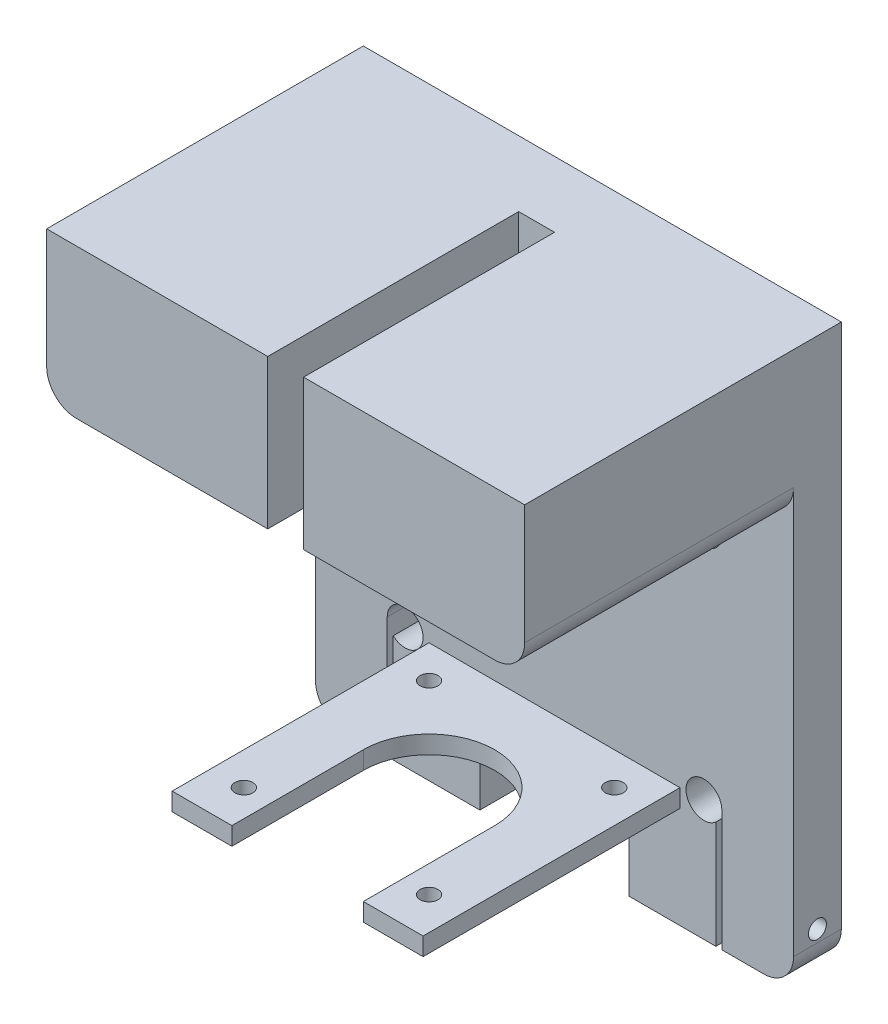
SolidWorks part; units mm, degrees
ref_plane "前视基准面" through (0, 0, 0) normal (0, 0, 1) x (1, 0, 0)
ref_plane "上视基准面" through (0, 0, 0) normal (0, 1, 0) x (1, 0, 0)
ref_plane "右视基准面" through (0, 0, 0) normal (1, 0, 0) x (0, 0, -1)
sketch "草图1" plane through (0, 0, 0) normal (0, 0, 1) x (1, 0, 0)
  line L1 (-40, -42.5) -> (40, -42.5)
  line L2 (-40, -42.5) -> (-40, 42.5)
  line L3 (-40, 42.5) -> (40, 42.5) construction
  line L4 (40, -42.5) -> (40, 42.5)
  line L5 (-40, -42.5) -> (40, 42.5) construction
  line L6 (-40, 42.5) -> (40, -42.5) construction
  line L7 (-40, 42.5) -> (40, 42.5) construction
  line L8 (-40, 42.5) -> (-40, 50.5)
  line L9 (-40, 50.5) -> (40, 50.5)
  line L10 (40, 42.5) -> (40, 50.5)
  point P0 (0, 0)
  dimension "D1" = 80
  dimension "D2" = 85
  dimension "D3" = 8
extrude "凸台-拉伸1" add sketch "草图1" along normal blind 8
sketch "草图3" plane through (0, 0, 8) normal (0, 0, 1) x (1, 0, 0)
  line L0 (0, 43.5088) -> (0, -56.4658) construction
  line L1 (-40, -42.5) -> (40, -42.5) construction
  line L2 (-21, -25.5) -> (21, -25.5)
  line L3 (-21, -25.5) -> (-21, -22.5)
  line L4 (-21, -22.5) -> (21, -22.5)
  line L5 (21, -25.5) -> (21, -22.5)
  line L6 (-21, -25.5) -> (21, -22.5) construction
  line L7 (-21, -22.5) -> (21, -25.5) construction
  point P3 (0, -24)
  dimension "D1" = 17
  dimension "D2" = 3
  dimension "D3" = 42
extrude "凸台-拉伸2" add sketch "草图3" along normal blind 43
sketch "草图4" plane through (0, -25.5, 0) normal (0, -1, 0) x (1, 0, 0)
  line L0 (0, 29) -> (-7.7782, 36.7782) construction
  line L1 (-15.5, 13.5) -> (-14, 13.5) construction
  line L2 (-15.5, 13.5) -> (-15.5, 15) construction
  line L3 (-15.5, 44.5) -> (-14, 44.5) construction
  line L4 (15.5, 13.5) -> (15.5, 15) construction
  line L5 (-15.5, 13.5) -> (-14.4393, 14.5607) construction
  line L6 (-15.5, 44.5) -> (-14.4393, 43.4393) construction
  line L7 (-14, 44.5) -> (14, 44.5) construction
  line L8 (14, 44.5) -> (15.5, 44.5) construction
  line L9 (-7.7782, 36.7782) -> (-14.4393, 43.4393) construction
  line L10 (-14.4393, 43.4393) -> (-15.5, 44.5) construction
  line L11 (-14.4393, 43.4393) -> (-7.7782, 36.7782) construction
  line L12 (0, 29) -> (7.7782, 21.2218) construction
  line L13 (-15.5, 15) -> (-15.5, 43) construction
  line L14 (-15.5, 43) -> (-15.5, 44.5) construction
  line L15 (-14.4393, 14.5607) -> (-7.7782, 21.2218) construction
  line L16 (-7.7782, 21.2218) -> (0, 29) construction
  line L17 (-14, 13.5) -> (14, 13.5) construction
  line L18 (14, 13.5) -> (15.5, 13.5) construction
  line L19 (7.7782, 21.2218) -> (14.4393, 14.5607) construction
  line L20 (14.4393, 14.5607) -> (15.5, 13.5) construction
  line L21 (15.5, 15) -> (15.5, 43) construction
  line L22 (15.5, 43) -> (15.5, 44.5) construction
  line L23 (14.4393, 43.4393) -> (15.5, 44.5) construction
  line L24 (-21, 8) -> (21, 8) construction
  line L26 (-11, 29) -> (-11, 51)
  line L27 (21, 51) -> (21, 8) construction
  line L28 (-21, 51) -> (21, 51) construction
  line L29 (-11, 51) -> (11, 51)
  line L30 (11, 51) -> (11, 29)
  line L31 (-7.7782, 36.7782) -> (0, 29) construction
  line L32 (0, 29) -> (7.7782, 36.7782) construction
  line L33 (7.7782, 36.7782) -> (14.4393, 43.4393) construction
  arc A0 (-11, 29) -> (11, 29) centre (0, 29) ccw
  circle A1 centre (-15.5, 44.5) radius 1.5
  circle A2 centre (15.5, 44.5) radius 1.5
  circle A3 centre (15.5, 13.5) radius 1.5
  circle A4 centre (-15.5, 13.5) radius 1.5
  arc A5 (7.7782, 36.7782) -> (-7.7782, 36.7782) centre (0, 29) ccw construction
  arc A6 (-7.7782, 36.7782) -> (-11, 29) centre (0, 29) ccw construction
  arc A7 (11, 29) -> (7.7782, 36.7782) centre (0, 29) ccw construction
  point P0 (0, 29)
  dimension "D5" = 3
  dimension "D6" = 11
  dimension "D1" = 31
  dimension "D2" = 36.5
  dimension "D4" = 21.9203
  dimension "D7" = 21
  dimension "D3" = 4
extrude "切除-拉伸1" cut sketch "草图4" against normal up to next
sketch "草图5" plane through (0, 0, 8) normal (0, 0, 1) x (1, 0, 0)
  line L0 (-21, -25.5) -> (21, -25.5) construction
  line L1 (-12.5, -25.5) -> (12.5, -25.5)
  line L2 (-12.5, -25.5) -> (-12.5, -42.5)
  line L3 (-12.5, -42.5) -> (12.5, -42.5)
  line L4 (0, -25.5) -> (0, -42.5) construction
  line L5 (-40, -42.5) -> (40, -42.5) construction
  line L6 (0, 33.1882) -> (0, -25.5) construction
  line L7 (12.5, -25.5) -> (12.5, -42.5)
  line L8 (0, -25.5) -> (0, -42.5) construction
  line L9 (0, -42.5) -> (0, -34.9776) construction
  dimension "D1" = 25
extrude "切除-拉伸2" cut sketch "草图5" against normal through all
sketch "草图7" plane through (0, 0, 8) normal (0, 0, 1) x (1, 0, 0)
  line L0 (-22, 17.5) -> (22, 17.5) construction
  line L1 (22, -17.5) -> (25, -17.5) construction
  line L2 (-25, -17.5) -> (-25, -14.5) construction
  line L3 (-25, 17.5) -> (-22, 17.5) construction
  line L4 (25, 14.5) -> (25, 17.5) construction
  line L5 (-22.5423, -15.7796) -> (22.5423, 15.7796) construction
  line L6 (-22.5423, 15.7796) -> (22.5423, -15.7796) construction
  line L7 (22, 17.5) -> (25, 17.5) construction
  line L8 (-25, 17.5) -> (-22.5423, 15.7796) construction
  line L9 (-25, 14.5) -> (-25, 17.5) construction
  line L10 (-25, -14.5) -> (-25, 14.5) construction
  line L11 (-25, -17.5) -> (-22.5423, -15.7796) construction
  line L12 (-40, -42.5) -> (-12.5, -42.5) construction
  line L14 (22.5423, -15.7796) -> (25, -17.5) construction
  line L15 (25, -17.5) -> (25, -14.5) construction
  line L16 (25, -14.5) -> (25, 14.5) construction
  line L17 (22.5423, 15.7796) -> (25, 17.5) construction
  line L18 (0, 0) -> (0, -4.8788) construction
  circle A0 centre (-25, 17.5) radius 3
  circle A1 centre (25, 17.5) radius 3
  circle A4 centre (-25, -22.25) radius 3
  circle A6 centre (25, -22.25) radius 3
  point P0 (0, 0)
  dimension "D3" = 6
  dimension "D4" = 6
  dimension "D5" = 25
  dimension "D6" = 20.25
  dimension "D1" = 50
  dimension "D2" = 35
extrude "切除-拉伸3" cut sketch "草图7" against normal through all
fillet "圆角1" radius 5 1 edges at (-40, -42.5, 4)
sketch "草图8" plane through (0, 0, 8) normal (0, 0, 1) x (1, 0, 0)
  line L1 (-35, -42.5) -> (-12.5, -42.5) construction
  line L4 (0, 35.1811) -> (0, -36.2727) construction
  line L9 (-28, -22.25) -> (-28, -42.5)
  line L10 (-28, -42.5) -> (-27, -42.5)
  line L11 (-27, -42.5) -> (-27, -24.4861)
  line L12 (28, -42.5) -> (27, -42.5)
  line L13 (27, -42.5) -> (27, -24.4861)
  line L15 (28, -22.25) -> (28, -42.5)
  circle A5 centre (-25, -22.25) radius 3 construction
  arc A7 (-28, -22.25) -> (-27, -24.4861) centre (-25, -22.25) ccw
  arc A8 (28, -22.25) -> (27, -24.4861) centre (25, -22.25) cw
  dimension "D2" = 1
extrude "切除-拉伸4" cut sketch "草图8" against normal through all
sketch "草图9" plane through (-40, 0, 0) normal (-1, 0, 0) x (0, 0, 1)
  line L0 (0, -37.5) -> (8, -37.5) construction
  circle A0 centre (4, -35.5) radius 1.5
  dimension "D1" = 3
  dimension "D2" = 2
extrude "切除-拉伸5" cut sketch "草图9" against normal through all both and the other way through all
sketch "草图12" plane through (0, 0, 8) normal (0, 0, 1) x (1, 0, 0)
  line L0 (40, -42.5) -> (40, 50.5) construction
  line L1 (-40, 50.5) -> (40, 50.5)
  line L2 (-40, 50.5) -> (-40, 25.5)
  line L3 (-40, 25.5) -> (40, 25.5)
  line L4 (40, 50.5) -> (40, 25.5)
  dimension "D1" = 25
extrude "凸台-拉伸4" add sketch "草图12" along normal blind 45
sketch "草图13" plane through (0, 0, 53) normal (0, 0, 1) x (1, 0, 0)
  line L0 (0, 50.5) -> (0, 19.3771) construction
  line L3 (40, 50.5) -> (-40, 50.5) construction
  line L4 (3, 50.5) -> (-3, 50.5)
  line L5 (-3, 50.5) -> (-3, 25.5)
  line L6 (-40, 25.5) -> (40, 25.5) construction
  line L7 (-3, 25.5) -> (3, 25.5)
  line L8 (-40, 25.5) -> (40, 25.5) construction
  line L9 (3, 50.5) -> (3, 25.5)
  point P13 (0, 25.5)
  dimension "D1" = 3
extrude "切除-拉伸6" cut sketch "草图13" against normal blind 42
fillet "圆角3" radius 5 2 edges at (40, 25.5, 30.5) (-40, 25.5, 30.5)
fillet "圆角4" radius 5 1 edges at (40, -42.5, 4)
